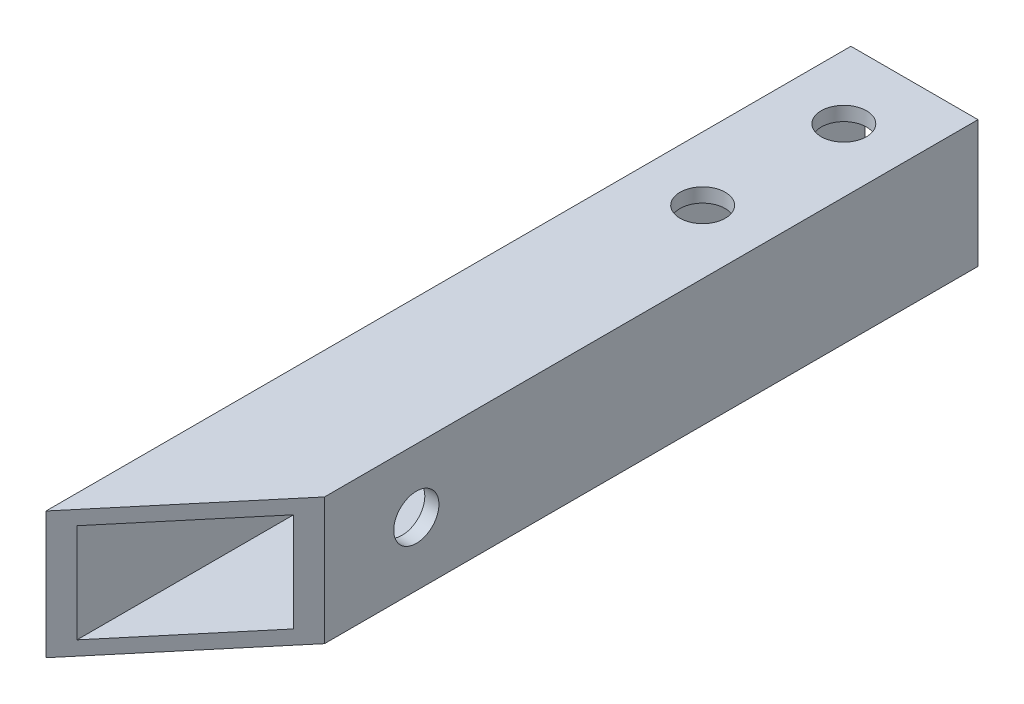
SolidWorks part; units mm, degrees
ref_plane "正面" through (0, 0, 0) normal (0, 0, 1) x (1, 0, 0)
ref_plane "平面" through (0, 0, 0) normal (0, 1, 0) x (1, 0, 0)
ref_plane "右側面" through (0, 0, 0) normal (1, 0, 0) x (0, 0, -1)
sketch "ｽｹｯﾁ1" plane through (0, 0, 0) normal (0, 0, 1) x (1, 0, 0)
  line L1 (-3.5, 3.5) -> (3.5, 3.5)
  line L2 (-3.5, 3.5) -> (-3.5, -3.5)
  line L3 (-3.5, -3.5) -> (3.5, -3.5)
  line L4 (3.5, 3.5) -> (3.5, -3.5)
  line L5 (-3.5, 3.5) -> (3.5, -3.5) construction
  line L6 (-3.5, -3.5) -> (3.5, 3.5) construction
  line L7 (-4.5, 4.5) -> (4.5, 4.5)
  line L8 (-4.5, 4.5) -> (-4.5, -4.5)
  line L9 (-4.5, -4.5) -> (4.5, -4.5)
  line L10 (4.5, 4.5) -> (4.5, -4.5)
  line L11 (-4.5, 4.5) -> (4.5, -4.5) construction
  line L12 (-4.5, -4.5) -> (4.5, 4.5) construction
  point P0 (0, 0)
  point P6 (0, 0)
  dimension "D1" = 7
  dimension "D2" = 7
  dimension "D3" = 9
  dimension "D4" = 9
extrude "ﾎﾞｽ - 押し出し1" add sketch "ｽｹｯﾁ1" along normal blind 70
sketch "ｽｹｯﾁ2" plane through (0, 4.5, 0) normal (0, 1, 0) x (1, 0, 0)
  line L0 (0, 0) -> (0, -5)
  line L1 (0, -5) -> (0, -15)
  circle A0 centre (0, -5) radius 1.6
  circle A1 centre (0, -15) radius 1.6
  dimension "D3" = 3.2
  dimension "D4" = 3.2
  dimension "D1" = 5
  dimension "D2" = 10
extrude "ｶｯﾄ - 押し出し1" cut sketch "ｽｹｯﾁ2" against normal blind 50
sketch "ｽｹｯﾁ3" plane through (0, 4.5, 0) normal (0, 1, 0) x (1, 0, 0)
  line L0 (-4.5, -70) -> (-4.5, -57)
  line L1 (-4.5, -70) -> (-4.5, 0) construction
  line L2 (-4.5, -57) -> (4.5, -57)
  line L3 (4.5, -70) -> (4.5, 0) construction
  line L4 (-4.5, -57) -> (8.8606, -41.0775)
  line L5 (8.8606, -41.0775) -> (4.5, -57)
  line L6 (4.5, -57) -> (4.5, -70)
  line L7 (4.5, -70) -> (-4.5, -70)
  line M9 (4.5, -70) -> (4.5, 0)
  dimension "D1" = 13
  dimension "D2" = 50
extrude "ｶｯﾄ - 押し出し2" cut sketch "ｽｹｯﾁ3" against normal blind 10 contours L4 L2 M9
sketch "ｽｹｯﾁ4" plane through (0, 4.5, 0) normal (0, 1, 0) x (1, 0, 0)
  line L1 (-4.5, -57) -> (4.5, -57)
  line L2 (-4.5, -57) -> (-4.5, -70)
  line L3 (-4.5, -70) -> (4.5, -70)
  line L4 (4.5, -57) -> (4.5, -70)
extrude "ｶｯﾄ - 押し出し3" cut sketch "ｽｹｯﾁ4" against normal blind 10
sketch "ｽｹｯﾁ5" plane through (4.5, 0, 0) normal (1, 0, 0) x (0, 0, -1)
  line L0 (-46.2742, 0) -> (-39.7742, 0)
  line L1 (-46.2742, -4.5) -> (-46.2742, 4.5) construction
  circle A0 centre (-39.7742, 0) radius 1.6
  dimension "D2" = 3.2
  dimension "D1" = 6.5
extrude "ｶｯﾄ - 押し出し4" cut sketch "ｽｹｯﾁ5" against normal blind 400
